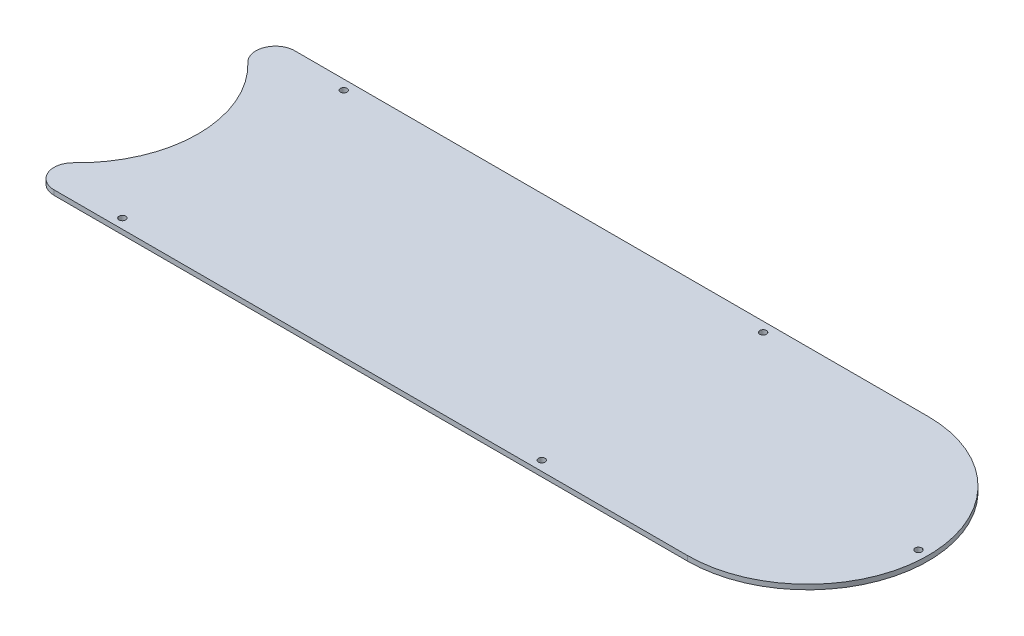
SolidWorks part; units mm, degrees
ref_plane "Front Plane" through (0, 0, 0) normal (0, 0, 1) x (1, 0, 0)
ref_plane "Top Plane" through (0, 0, 0) normal (0, 1, 0) x (1, 0, 0)
ref_plane "Right Plane" through (0, 0, 0) normal (1, 0, 0) x (0, 0, -1)
sketch "Sketch1" plane through (0, 0, 0) normal (0, 1, 0) x (1, 0, 0)
  line L0 (0, 0) -> (238.76, 0) construction
  line L1 (238.76, 39.37) -> (0, 39.37)
  line L2 (0, -39.37) -> (238.76, -39.37)
  arc A0 (0, -39.37) -> (0, 39.37) centre (0, 0) ccw
  arc A1 (238.76, -39.37) -> (238.76, 39.37) centre (238.76, 0) ccw
  circle A2 centre (274.955, 0) radius 1.0922
  circle A3 centre (187.96, 36.195) radius 1.0922
  circle A4 centre (50.8, 36.195) radius 1.0922
  circle A5 centre (50.8, -36.195) radius 1.0922
  circle A6 centre (187.96, -36.195) radius 1.0922
  dimension "D1" = 78.74
  dimension "D3" = 2.1844
  dimension "D2" = 238.76
  dimension "D4" = 3.175
  dimension "D5" = 3.175
  dimension "D6" = 50.8
  dimension "D7" = 50.8
extrude "Boss-Extrude1" add sketch "Sketch1" along normal blind 1.5875
fillet "Fillet1" radius 6.35 2 edges at (0, 0.7937, 39.37) (0, 0.7937, -39.37)
